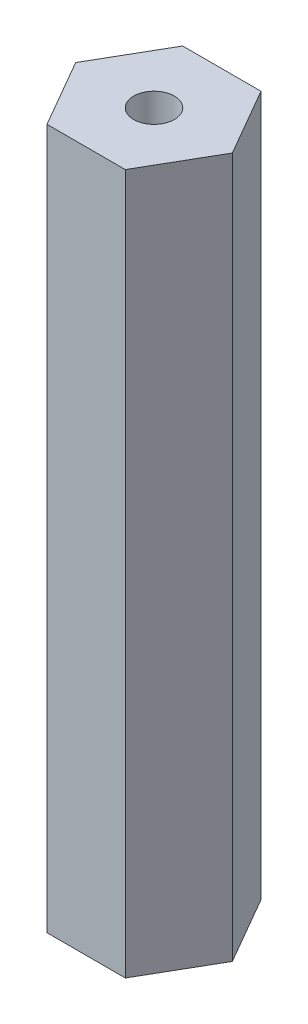
SolidWorks part; units mm, degrees
ref_plane "Спереди" through (0, 0, 0) normal (0, 0, 1) x (1, 0, 0)
ref_plane "Сверху" through (0, 0, 0) normal (0, 1, 0) x (1, 0, 0)
ref_plane "Справа" through (0, 0, 0) normal (1, 0, 0) x (0, 0, -1)
sketch "Эскиз1" plane through (0, 0, 0) normal (0, 1, 0) x (1, 0, 0)
  line L1 (2.8868, 0) -> (1.4434, 2.5)
  line L2 (1.4434, 2.5) -> (-1.4434, 2.5)
  line L3 (-1.4434, 2.5) -> (-2.8868, 0)
  line L4 (-2.8868, 0) -> (-1.4434, -2.5)
  line L5 (-1.4434, -2.5) -> (1.4434, -2.5)
  line L6 (1.4434, -2.5) -> (2.8868, 0)
  circle A0 centre (0, 0) radius 2.5 construction
  dimension "D1" = 5
extrude "Бобышка-Вытянуть1" add sketch "Эскиз1" along normal up to surface (25.8 mm away)
sketch "Эскиз2" plane through (0, 25.8, 0) normal (0, 1, 0) x (1, 0, 0)
  circle A0 centre (0, 0) radius 0.75
  dimension "D1" = 1.5
extrude "Вырез-Вытянуть1" cut sketch "Эскиз2" against normal through all
